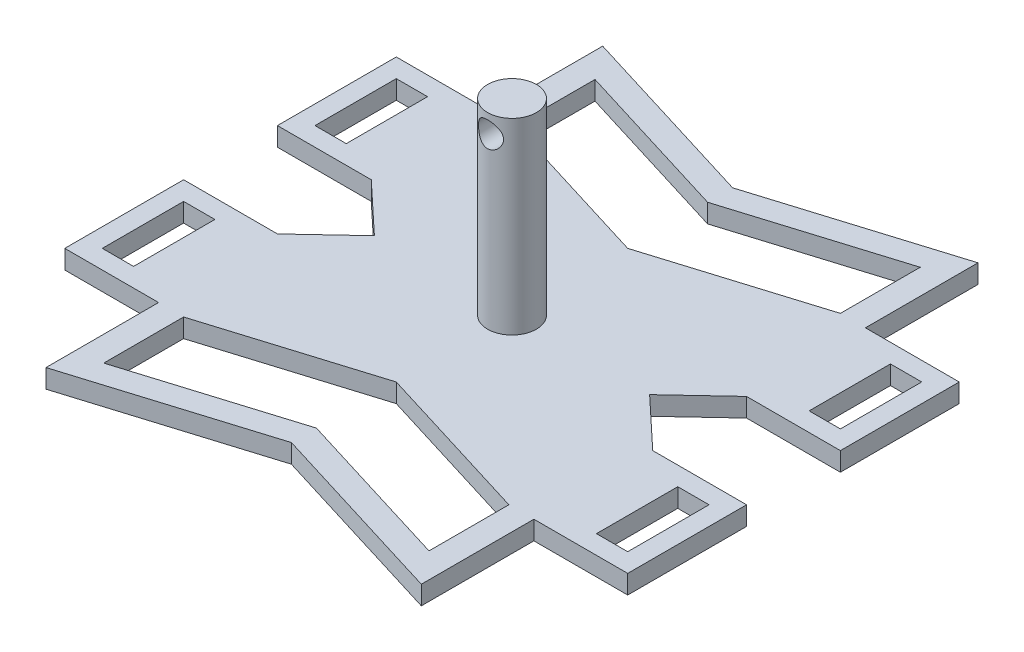
SolidWorks part; units mm, degrees
ref_plane "Alzado" through (0, 0, 0) normal (0, 0, 1) x (1, 0, 0)
ref_plane "Planta" through (0, 0, 0) normal (0, 1, 0) x (1, 0, 0)
ref_plane "Vista lateral" through (0, 0, 0) normal (1, 0, 0) x (0, 0, -1)
sketch "Croquis1" plane through (0, 0, 0) normal (0, 1, 0) x (1, 0, 0)
  line L0 (-45, -26.5) -> (-30, -26.5)
  line L1 (26, 26.5) -> (-26, 26.5) construction
  line L2 (30, -26.5) -> (30, -7.5) construction
  line L3 (26, -26.5) -> (-26, -26.5) construction
  line L4 (30, 7.5) -> (30, 26.5) construction
  line L5 (-30, -26.5) -> (30, 26.5) construction
  line L6 (30, -26.5) -> (-30, 26.5) construction
  line L7 (30, -26.5) -> (45, -26.5)
  line L8 (45, -26.5) -> (45, -7.5)
  line L9 (45, -7.5) -> (30, -7.5)
  line L10 (30, -7.5) -> (30, 7.5) construction
  line L11 (30, 7.5) -> (45, 7.5)
  line L12 (45, 7.5) -> (45, 26.5)
  line L13 (45, 26.5) -> (30, 26.5)
  line L14 (0, -18.5) -> (26, -26.5)
  line L15 (0, -18.5) -> (-26, -26.5)
  line L16 (-30, 26.5) -> (-45, 26.5)
  line L17 (-45, 26.5) -> (-45, 7.5)
  line L18 (-45, 7.5) -> (-30, 7.5)
  line L19 (-30, 7.5) -> (-30, -7.5) construction
  line L20 (-30, -7.5) -> (-45, -7.5)
  line L21 (-45, -7.5) -> (-45, -26.5)
  line L22 (-30, -7.5) -> (-22, 0)
  line L23 (-22, 0) -> (-30, 7.5)
  line L24 (-30, 7.5) -> (-30, 26.5) construction
  line L25 (-30, -26.5) -> (-30, -7.5) construction
  line L26 (26, 26.5) -> (0, 18.5)
  line L27 (0, 18.5) -> (-26, 26.5)
  line L28 (30, 7.5) -> (22, 0)
  line L29 (22, 0) -> (30, -7.5)
  line L30 (42, -10.5) -> (45, -10.5) construction
  line L31 (42, -10.5) -> (37, -10.5)
  line L32 (42, -10.5) -> (42, -23.5)
  line L33 (42, -23.5) -> (37, -23.5)
  line L34 (37, -10.5) -> (37, -23.5)
  line L35 (42, -10.5) -> (42, -7.5) construction
  line L36 (42, -23.5) -> (42, -26.5) construction
  line L37 (-42, 23.5) -> (-42, 26.5) construction
  line L38 (42, 23.5) -> (37, 23.5)
  line L39 (42, 23.5) -> (42, 10.5)
  line L40 (42, 10.5) -> (37, 10.5)
  line L41 (37, 23.5) -> (37, 10.5)
  line L42 (-42, 23.5) -> (-37, 23.5)
  line L43 (-42, 23.5) -> (-42, 10.5)
  line L44 (-42, 10.5) -> (-37, 10.5)
  line L45 (-37, 23.5) -> (-37, 10.5)
  line L46 (-42, -10.5) -> (-37, -10.5)
  line L47 (-42, -10.5) -> (-42, -23.5)
  line L48 (-42, -23.5) -> (-37, -23.5)
  line L49 (-37, -10.5) -> (-37, -23.5)
  line L50 (-42, 23.5) -> (-45, 23.5) construction
  line L51 (-42, -10.5) -> (-45, -10.5) construction
  line L52 (-42, -10.5) -> (-42, -7.5) construction
  line L53 (42, 23.5) -> (42, 26.5) construction
  line L54 (42, 23.5) -> (45, 23.5) construction
  line L55 (30, -26.5) -> (30, -50.5) construction
  line L56 (30, -50.5) -> (-30, -50.5) construction
  line L57 (-30, -50.5) -> (-30, -26.5) construction
  line L58 (-30, 26.5) -> (-30, 50.5) construction
  line L59 (-30, 50.5) -> (30, 50.5) construction
  line L60 (30, 50.5) -> (30, 26.5) construction
  line L61 (30, -26.5) -> (30, -44.5)
  line L62 (30, -44.5) -> (0, -35.2692)
  line L63 (0, -35.2692) -> (-30, -44.5)
  line L64 (-30, -44.5) -> (-30, -26.5)
  line L65 (30, 26.5) -> (30, 44.5)
  line L66 (30, 44.5) -> (0, 35.2692)
  line L67 (0, 35.2692) -> (-30, 44.5)
  line L68 (-30, 44.5) -> (-30, 26.5)
  line L69 (0, -50.5) -> (0, -35.2692) construction
  line L70 (0, 35.2692) -> (0, 50.5) construction
  line L71 (26, -26.5) -> (26, -39.2692)
  line L72 (26, -39.2692) -> (0, -31.2692)
  line L73 (0, -31.2692) -> (-26, -39.2692)
  line L74 (-26, -39.2692) -> (-26, -26.5)
  line L75 (0, -31.2692) -> (0, -35.2692) construction
  line L76 (26, -26.5) -> (30, -26.5) construction
  line L77 (-26, -26.5) -> (-30, -26.5) construction
  line L78 (-26, 26.5) -> (-26, 39.2692)
  line L79 (-26, 39.2692) -> (0, 31.2692)
  line L80 (0, 31.2692) -> (26, 39.2692)
  line L81 (26, 39.2692) -> (26, 26.5)
  line L82 (26, 26.5) -> (30, 26.5) construction
  line L83 (-26, 26.5) -> (-30, 26.5) construction
  line L84 (0, 31.2692) -> (0, 35.2692) construction
  line L85 (0, -18.5) -> (0, -26.5) construction
  line L86 (0, 18.5) -> (0, 26.5) construction
  line L87 (0, -31.2692) -> (0, -26.5) construction
  line L88 (0, 31.2692) -> (0, 26.5) construction
  line L90 (-26, -39.2692) -> (-26.619, -39.3517) construction
  point P0 (0, 0)
  point P1 (0, 0)
  point P48 (42, -17)
  point P49 (42, 17)
  point P50 (39.5, -10.5)
  point P52 (0, -50.5)
  point P56 (0, 50.5)
  dimension "D6" = 3
  dimension "D1" = 60
  dimension "D2" = 34
  dimension "D3" = 13
  dimension "D4" = 9.5
  dimension "D5" = 4
  dimension "D7" = 8
  dimension "D8" = 5
  dimension "D9" = 101
  dimension "D10" = 8
  dimension "D11" = 18
  dimension "D12" = 8
extrude "Saliente-Extruir1" add sketch "Croquis1" along normal blind 3
sketch "Croquis9" plane through (0, 3, 0) normal (0, 1, 0) x (1, 0, 0)
  circle A0 centre (0, 0) radius 3.9
  dimension "D1" = 7.8
extrude "Saliente-Extruir2" add sketch "Croquis9" along normal blind 30
sketch "Croquis10" plane through (0, 0, 0) normal (0, 0, 1) x (1, 0, 0)
  line L0 (0, 0) -> (0, 30) construction
  circle A0 centre (0, 30) radius 2
  dimension "D1" = 4
  dimension "D2" = 30
extrude "Cortar-Extruir7" cut sketch "Croquis10" against normal through all and the other way through all
